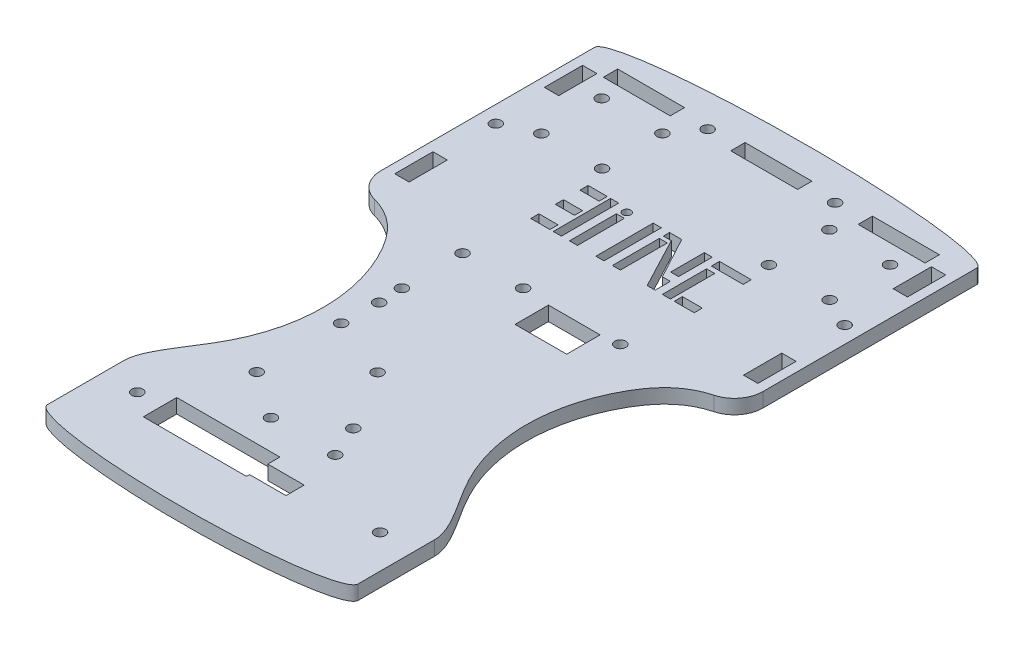
SolidWorks part; units mm, degrees
ref_plane "Front Plane" through (0, 0, 0) normal (0, 0, 1) x (1, 0, 0)
ref_plane "Top Plane" through (0, 0, 0) normal (0, 1, 0) x (1, 0, 0)
ref_plane "Right Plane" through (0, 0, 0) normal (1, 0, 0) x (0, 0, -1)
sketch "Sketch1" plane through (0, 0, 0) normal (0, 1, 0) x (1, 0, 0)
  line L1 (40, 50) -> (-40, 50)
  line L2 (40, 50) -> (40, -50)
  line L3 (40, -50) -> (-40, -50)
  line L4 (-40, 50) -> (-40, -50)
  line L5 (40, 50) -> (-40, -50) construction
  line L6 (40, -50) -> (-40, 50) construction
  point P0 (0, 0)
  dimension "D1" = 80
  dimension "D2" = 100
extrude "Boss-Extrude1" add sketch "Sketch1" along normal mid plane 3
sketch "Sketch2" plane through (0, 1.5, 0) normal (0, 1, 0) x (1, 0, 0)
  line L0 (0, 50) -> (0, 32.5) construction
  line L1 (40, 50) -> (-40, 50) construction
  line L2 (-7, 47) -> (-13.3333, 47) construction
  line L3 (-40, 50) -> (-40, -50) construction
  line L4 (-13.3333, 47) -> (-19.6667, 47) construction
  line L5 (-13.3333, 47) -> (-13.3333, 48.15) construction
  line L6 (-33.6667, 48.5) -> (-19.6667, 48.5)
  line L7 (-33.6667, 48.5) -> (-33.6667, 45.5)
  line L8 (-33.6667, 45.5) -> (-19.6667, 45.5)
  line L9 (-19.6667, 48.5) -> (-19.6667, 45.5)
  line L10 (-13.3333, 48.15) -> (-19.6667, 48.15) construction
  line L11 (-33.6667, 48.15) -> (-40, 48.15) construction
  line L12 (0, 47) -> (7, 48.5) construction
  line L13 (7, 48.5) -> (-7, 48.5)
  line L14 (0, 47) -> (7, 45.5) construction
  line L15 (7, 45.5) -> (-7, 45.5)
  line L16 (-7, 48.5) -> (-7, 45.5)
  line L17 (0, 47) -> (-7, 45.5) construction
  line L18 (0, 47) -> (-7, 48.5) construction
  line L19 (13.3333, 48.15) -> (19.6667, 48.15) construction
  line L20 (13.3333, 47) -> (13.3333, 48.15) construction
  line L21 (13.3333, 47) -> (19.6667, 47) construction
  line L22 (7, 47) -> (13.3333, 47) construction
  line L23 (7, 48.5) -> (7, 45.5)
  line L24 (19.6667, 48.5) -> (19.6667, 45.5)
  line L25 (33.6667, 45.5) -> (19.6667, 45.5)
  line L26 (33.6667, 48.5) -> (33.6667, 45.5)
  line L27 (33.6667, 48.5) -> (19.6667, 48.5)
  circle A0 centre (-13.3333, 47) radius 1.15
  circle A1 centre (13.3333, 47) radius 1.15
  point P25 (0, 48.5)
  point P34 (0, 45.5)
  dimension "D1" = 2.3
  dimension "D2" = 3
  dimension "D3" = 3
  dimension "D4" = 3
  dimension "D5" = 14
  dimension "D6" = 7
extrude "Cut-Extrude1" cut sketch "Sketch2" against normal through all
sketch "Sketch3" plane through (0, 1.5, 0) normal (0, 1, 0) x (1, 0, 0)
  line L0 (36.5, 24.6918) -> (36.5, 26.9918) construction
  line L1 (-35, 45.5) -> (-38, 45.5)
  line L2 (-35, 45.5) -> (-35, 37.5)
  line L3 (-35, 37.5) -> (-38, 37.5)
  line L4 (-38, 45.5) -> (-38, 37.5)
  line L5 (-35, 14.1836) -> (-38, 14.1836)
  line L6 (-35, 14.1836) -> (-35, 6.1836)
  line L7 (-35, 6.1836) -> (-38, 6.1836)
  line L8 (-38, 14.1836) -> (-38, 6.1836)
  line L9 (38, 14.1836) -> (35, 14.1836)
  line L10 (38, 14.1836) -> (38, 6.1836)
  line L11 (38, 6.1836) -> (35, 6.1836)
  line L12 (35, 14.1836) -> (35, 6.1836)
  line L13 (35, 37.5) -> (38, 37.5)
  line L14 (35, 37.5) -> (35, 45.5)
  line L15 (35, 45.5) -> (38, 45.5)
  line L16 (38, 37.5) -> (38, 45.5)
  line L17 (38, 24.6918) -> (35, 24.6918) construction
  line L18 (38, 26.9918) -> (35, 26.9918) construction
  line L19 (-36.5, 26.9918) -> (-36.5, 24.6918) construction
  line L20 (-35, 26.9918) -> (-38, 26.9918) construction
  line L21 (-35, 24.6918) -> (-38, 24.6918) construction
  circle A0 centre (36.5, 25.8418) radius 1.15
  circle A1 centre (-36.5, 25.8418) radius 1.15
  dimension "D1" = 2.3
  dimension "D2" = 2.3
extrude "Cut-Extrude2" cut sketch "Sketch3" against normal through all
sketch "Sketch5" plane through (0, 1.5, 0) normal (0, 1, 0) x (1, 0, 0)
  line L0 (40, 50) -> (-40, 50) construction
  line L1 (40, 50) -> (-40, 50)
  ellipse E0 centre (0, 50) end of major axis (-40, 50) minor radius 4.5 (40, 50) -> (-40, 50) ccw
  dimension "D1" = 4.5
extrude "Boss-Extrude2" add sketch "Sketch5" against normal up to vertex (3 mm away)
sketch "Sketch6" plane through (0, -1.5, 0) normal (0, -1, 0) x (1, 0, 0)
  line L0 (0, 0) -> (0, 50) construction
  line L1 (-40, 50) -> (40, 50) construction
sketch "Sketch9" plane through (0, 1.5, 0) normal (0, 1, 0) x (1, 0, 0)
  line L0 (40, -50) -> (40, 50) construction
  line L1 (-40, -50) -> (40, -50)
  line L2 (-40, -50) -> (-40, -56)
  line L3 (-40, -56) -> (40, -56)
  line L4 (40, -50) -> (40, -56)
  dimension "D1" = 6
extrude "Boss-Extrude3" add sketch "Sketch9" against normal up to vertex (3 mm away)
sketch "Sketch7" plane through (0, 1.5, 0) normal (0, 1, 0) x (1, 0, 0)
  line L2 (40, 0) -> (67.1145, 0) construction
  line L3 (32.5, -56) -> (32.5, -57.6455) construction
  line L4 (40, 0) -> (40, -56)
  line L5 (40, -56) -> (32.5, -56)
  line L6 (0, 0) -> (0, -51.1929) construction
  line L7 (-32.5, -56) -> (-32.5, -57.6455) construction
  line L8 (-40, -56) -> (-32.5, -56)
  line L9 (-40, 0) -> (-40, -56)
  line L10 (40, -56) -> (40, 50) construction
  line L11 (-40, -56) -> (40, -56) construction
  spline S0 degree 3 poles (40, 0) (32.0981, 0) (20.5513, -12.4671) (19.3397, -36.9328) (32.5, -51.978) (32.5, -56) knots 0 0 0 0 0.26869 0.752948 1 1 1 1
  spline S1 degree 3 poles (-40, 0) (-32.0981, 0) (-20.5513, -12.4671) (-19.3397, -36.9328) (-32.5, -51.978) (-32.5, -56) knots 0 0 0 0 0.26869 0.752948 1 1 1 1
  dimension "D1" = 65
extrude "Cut-Extrude4" cut sketch "Sketch7" against normal through all
sketch "Sketch11" plane through (0, -1.5, 0) normal (0, -1, 0) x (1, 0, 0)
  line L0 (32.5, 56) -> (32.5, 72)
  line L1 (-32.5, 56) -> (-32.5, 72)
  line L2 (-32.5, 56) -> (32.5, 56)
  ellipse E0 centre (0, 72) end of major axis (32.5, 72) minor radius 4.5 (32.5, 72) -> (-32.5, 72) ccw
  point P7 (0, 56)
  dimension "D1" = 4.5
  dimension "D2" = 16
extrude "Boss-Extrude4" add sketch "Sketch11" against normal up to vertex (3 mm away)
sketch "Sketch12" plane through (0, 1.5, 0) normal (0, 1, 0) x (1, 0, 0)
  circle A0 centre (-6.731, -51) radius 1.143
  circle A1 centre (6.731, -51) radius 1.143
  circle A2 centre (6.731, -51) radius 1.143 construction
  circle A3 centre (-6.731, -51) radius 1.143 construction
extrude "Cut-Extrude5" cut sketch "Sketch12" against normal through all
sketch "Sketch13" plane through (0, 1.5, 0) normal (0, 1, 0) x (1, 0, 0)
  circle A0 centre (25.46, -60.3564) radius 1.15
  circle A1 centre (-25.34, -60.3564) radius 1.15
  dimension "D1" = 2.3
extrude "Cut-Extrude6" cut sketch "Sketch13" against normal through all
sketch "Sketch15" plane through (0, -1.5, 0) normal (0, -1, 0) x (1, 0, 0)
  line L0 (-18.355, 59.0864) -> (-18.355, 57.1814) construction
  line L1 (1.33, 57.1814) -> (-20.26, 57.1814)
  line L2 (8.95, 59.7214) -> (8.95, 63.5314)
  line L3 (8.95, 63.5314) -> (-20.26, 63.5314)
  line L4 (-20.26, 57.1814) -> (-20.26, 63.5314)
  line L5 (-18.355, 59.0864) -> (-20.26, 59.0864) construction
  line L6 (7.045, 61.6264) -> (7.045, 63.5314) construction
  line L7 (7.045, 61.6264) -> (8.95, 61.6264) construction
  line L8 (8.95, 59.7214) -> (1.33, 59.7214)
  line L9 (1.33, 59.7214) -> (1.33, 57.1814)
  line L10 (7.045, 61.6264) -> (7.045, 59.7214) construction
  line L11 (-0.575, 59.0864) -> (1.33, 59.0864) construction
  line L12 (-0.575, 59.0864) -> (-0.575, 57.1814) construction
  dimension "D1" = 1.905
extrude "Cut-Extrude7" cut sketch "Sketch15" against normal through all
fillet "Fillet1" radius 6 2 edges at (40, 0, 0) (-40, 0, 0)
sketch "Sketch16" plane through (0, -1.5, 0) normal (0, -1, 0) x (1, 0, 0)
  line L0 (-3.81, 1.1264) -> (-3.81, 44.195) construction
  line L1 (-3.81, 44.195) -> (-16.4994, 44.195) construction
  line L2 (-3.81, 22.6607) -> (-12.7886, 22.6607) construction
  line L3 (-3.81, 1.1264) -> (-16.2968, 1.1264) construction
  line L4 (-16.2968, 1.1264) -> (-16.2968, 18.7958) construction
  circle A0 centre (-16.4994, 44.195) radius 1.15
  circle A1 centre (-16.51, 13.8264) radius 1.15
  circle A2 centre (16.51, 1.1264) radius 1.15
  circle A3 centre (3.81, 44.3064) radius 1.15
  circle A4 centre (-3.81, 1.1264) radius 1.15
  circle A5 centre (-16.2968, 18.7958) radius 1.15
  circle A6 centre (-16.51, 1.1264) radius 1.15
  circle A7 centre (-16.51, 26.5264) radius 1.15
  circle A8 centre (-3.81, 31.6064) radius 1.15
  circle A9 centre (-16.51, 44.3064) radius 1.15
  dimension "D1" = 2.3
  dimension "D2" = 2.3
  dimension "D3" = 2.3
extrude "Cut-Extrude8" cut sketch "Sketch16" against normal through all contours A1 | A5 | A7 | A3 | A4 | A2 | A6 | A8 | A0
sketch "Sketch18" plane through (0, 1.5, 0) normal (0, 1, 0) x (1, 0, 0)
  line L0 (-36.5, 45.5) -> (-36.5, 37.5) construction
  line L1 (-35, 45.5) -> (-38, 45.5) construction
  line L2 (-38, 37.5) -> (-35, 37.5) construction
  circle A2 centre (-30.0025, 41.5) radius 1.15
  circle A3 centre (-29.9481, 28.8048) radius 1.15
  circle A4 centre (-17.2993, 41.5022) radius 1.15
  circle A5 centre (-17.2448, 28.807) radius 1.15
  circle A6 centre (17.6221, 41.5132) radius 1.15
  circle A7 centre (17.6766, 28.8181) radius 1.15
  circle A8 centre (30.3253, 41.5154) radius 1.15
  circle A9 centre (30.3798, 28.8203) radius 1.15
extrude "Cut-Extrude10" cut sketch "Sketch18" against normal blind 10
sketch "Sketch20" plane through (0, 1.5, 0) normal (0, 1, 0) x (1, 0, 0)
  line L21 (10.3479, 12.335) -> (11.8479, 12.335) construction
  line L66 (-10.9533, 24.3055) -> (-9.2533, 24.3055)
  line L67 (-10.9533, 24.3055) -> (-10.9533, 12.3055)
  line L68 (-10.9533, 12.3055) -> (-9.2533, 12.3055)
  line L69 (-9.2533, 24.3055) -> (-9.2533, 12.3055)
  line L70 (-11.6547, 19.1546) -> (-15.6547, 19.1546)
  line L71 (-11.6535, 24.3055) -> (-15.6535, 24.3055)
  line L72 (-11.6535, 24.3055) -> (-11.6535, 22.6055)
  line L73 (-11.6535, 22.6055) -> (-15.6535, 22.6055)
  line L74 (-15.6535, 24.3055) -> (-15.6535, 22.6055)
  line L75 (-11.6547, 19.1546) -> (-11.6547, 17.4546)
  line L76 (-11.6547, 17.4546) -> (-15.6547, 17.4546)
  line L77 (-15.6547, 19.1546) -> (-15.6547, 17.4546)
  line L78 (-11.6587, 14.0126) -> (-15.6587, 14.0126)
  line L79 (-11.6587, 14.0126) -> (-11.6587, 12.3126)
  line L80 (-11.6587, 12.3126) -> (-15.6587, 12.3126)
  line L81 (-15.6587, 14.0126) -> (-15.6587, 12.3126)
  line L82 (11.8636, 21.5894) -> (13.5636, 21.5894)
  line L83 (11.8636, 21.5894) -> (11.8636, 12.3131)
  line L84 (11.8636, 12.3131) -> (13.5636, 12.3131)
  line L85 (13.5636, 21.5894) -> (13.5636, 12.3131)
  line L86 (-7.5566, 22.1335) -> (-5.8879, 22.1335)
  line L87 (-7.5566, 22.1335) -> (-7.5566, 12.3071)
  line L88 (-7.5566, 12.3071) -> (-5.8879, 12.3071)
  line L89 (-5.8879, 22.1335) -> (-5.8879, 12.3071)
  line L90 (11.8636, 24.2872) -> (18.5147, 24.2872)
  line L91 (11.8636, 24.2872) -> (11.8636, 22.5872)
  line L92 (-2.0153, 24.2909) -> (-0.3153, 24.2909)
  line L93 (-2.0153, 24.2909) -> (-2.0153, 12.2909)
  line L94 (-2.0153, 12.2909) -> (-0.3153, 12.2909)
  line L95 (-0.3153, 24.2909) -> (-0.3153, 12.2909)
  line L96 (11.8636, 22.5872) -> (18.5147, 22.5872)
  line L97 (18.5147, 24.2872) -> (18.5147, 22.5872)
  line L98 (14.3619, 14.0234) -> (18.5408, 14.0234)
  line L99 (14.3619, 14.0234) -> (14.3619, 12.3234)
  line L100 (14.3619, 12.3234) -> (18.5408, 12.3234)
  line L101 (1.401, 22.1615) -> (3.0698, 22.1615)
  line L102 (1.401, 22.1615) -> (1.401, 12.335)
  line L103 (1.401, 12.335) -> (3.0698, 12.335)
  line L104 (3.0698, 22.1615) -> (3.0698, 12.335)
  line L105 (18.5408, 14.0234) -> (18.5408, 12.3234)
  line L106 (1.401, 24.2909) -> (1.401, 22.9878)
  line L107 (1.401, 22.9878) -> (3.0698, 22.9878)
  line L108 (3.0698, 22.9878) -> (8.6792, 12.335)
  line L109 (8.6792, 12.335) -> (10.3479, 12.335)
  line L110 (1.401, 24.2909) -> (3.9516, 24.2909)
  line L111 (3.9516, 24.2909) -> (8.6792, 15.5189)
  line L112 (8.6792, 15.5189) -> (10.3479, 15.5189)
  line L113 (10.3479, 15.5189) -> (10.3479, 12.335)
  line L114 (8.6872, 24.2909) -> (8.6872, 17.2352)
  line L115 (8.6872, 17.2352) -> (10.3479, 17.2352)
  line L116 (10.3479, 17.2352) -> (10.3479, 24.2909)
  line L117 (10.3479, 24.2909) -> (8.6872, 24.2909)
  circle A2 centre (-6.7222, 23.4555) radius 0.85
  circle A3 centre (-6.7222, 23.4555) radius 0.85
extrude "Cut-Extrude14" cut sketch "Sketch20" against normal blind 10 contours L89 L86 L87 L88 | L95 L92 L93 L94 | L104 L101 L102 L103 | L113 L112 L111 L110 L106 L107 L108 L109 | A2 | L71 L74 L73 L72 | L69 L66 L67 L68 | L70 L77 L76 L75 | L78 L81 L80 L79 | L116 L117 L114 L115 | L85 L82 L83 L84 | L97 L90 L91 L96 | L105 L98 L99 L100
sketch "Sketch21" plane through (0, 1.5, 0) normal (0, 1, 0) x (1, 0, 0)
  line L1 (1.8915, -1.5282) -> (12.6915, -1.5282)
  line L2 (1.8915, -1.5282) -> (1.8915, -8.5282)
  line L3 (1.8915, -8.5282) -> (12.6915, -8.5282)
  line L4 (12.6915, -1.5282) -> (12.6915, -8.5282)
  line L7 (-20.26, -63.5314) -> (1.33, -63.5314)
  line L8 (-20.26, -63.5314) -> (-20.26, -64.1814)
  line L9 (-20.26, -64.1814) -> (1.33, -64.1814)
  line L10 (1.33, -63.5314) -> (1.33, -64.1814)
extrude "Cut-Extrude16" cut sketch "Sketch21" against normal blind 10 contours L4 L1 L2 L3 | L10 L7 L8 L9
